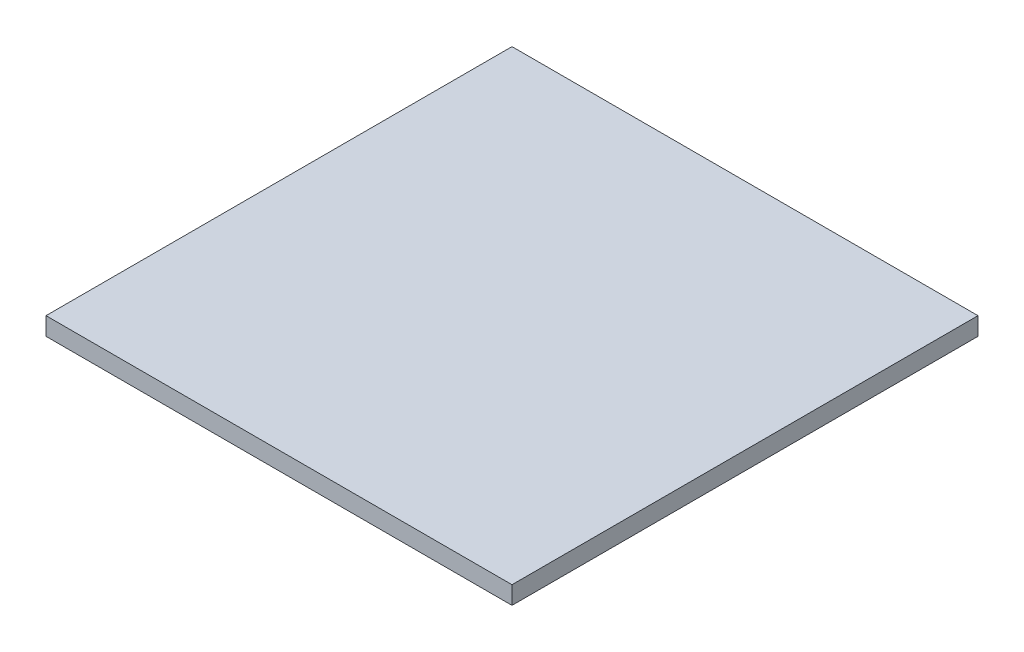
SolidWorks part; units mm, degrees
ref_plane "Front Plane" through (0, 0, 0) normal (0, 0, 1) x (1, 0, 0)
ref_plane "Top Plane" through (0, 0, 0) normal (0, 1, 0) x (1, 0, 0)
ref_plane "Right Plane" through (0, 0, 0) normal (1, 0, 0) x (0, 0, -1)
sketch "Sketch1" plane through (0, 0, 0) normal (0, 1, 0) x (1, 0, 0)
  line L1 (-60.6548, 121.5679) -> (104.4452, 121.5679)
  line L2 (-60.6548, 121.5679) -> (-60.6548, -43.5321)
  line L3 (-60.6548, -43.5321) -> (104.4452, -43.5321)
  line L4 (104.4452, 121.5679) -> (104.4452, -43.5321)
  dimension "D1" = 165.1
  dimension "D2" = 165.1
extrude "Boss-Extrude1" add sketch "Sketch1" along normal blind 6.35
